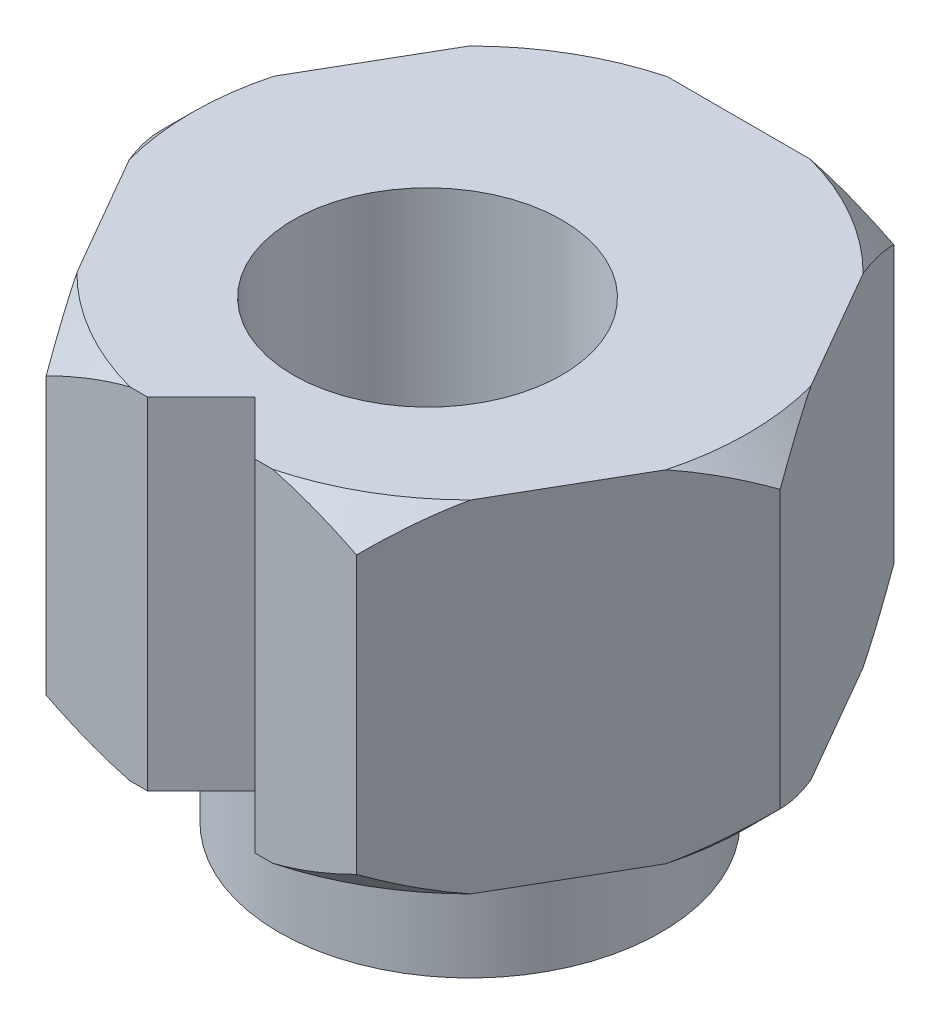
SolidWorks part; units mm, degrees
material "AISI 304"
ref_plane "Front Plane" through (0, 0, 0) normal (0, 0, 1) x (1, 0, 0)
ref_plane "Top Plane" through (0, 0, 0) normal (0, 1, 0) x (1, 0, 0)
ref_plane "Right Plane" through (0, 0, 0) normal (1, 0, 0) x (0, 0, -1)
sketch "Sketch1" plane through (0, 0, 0) normal (0, 1, 0) x (1, 0, 0)
  line L1 (5.7735, 0) -> (2.8868, 5)
  line L2 (2.8868, 5) -> (-2.8868, 5)
  line L3 (-2.8868, 5) -> (-5.7735, 0)
  line L4 (-5.7735, 0) -> (-2.8868, -5)
  line L5 (-2.8868, -5) -> (2.8868, -5)
  line L6 (2.8868, -5) -> (5.7735, 0)
  circle A0 centre (0, 0) radius 5 construction
  dimension "D1" = 10
extrude "Boss-Extrude1" add sketch "Sketch1" along normal blind 6.35
sketch "Sketch3" plane through (0, 0, 0) normal (0, -1, 0) x (1, 0, 0)
  circle A0 centre (0, 0) radius 3.555
  dimension "D1" = 7.11
extrude "Boss-Extrude3" add sketch "Sketch3" along normal blind 2.5
sketch "Sketch4" plane through (0, 6.35, 0) normal (0, 1, 0) x (1, 0, 0)
  line L0 (0, 0) -> (0, -0.79) construction
  circle A0 centre (0, -0.79) radius 2.5
  dimension "D1" = 5
  dimension "D2" = 0.79
extrude "Cut-Extrude1" cut sketch "Sketch4" against normal through all
sketch "Sketch5" plane through (0, 0, 0) normal (0, -1, 0) x (-1, 0, 0)
  line L0 (2.8868, -5) -> (-2.8868, -5) construction
  line L1 (-1, -5) -> (1, -5)
  line L2 (-1, -5) -> (0, -4)
  line L4 (1, -5) -> (0, -4)
  line L5 (0, -5) -> (0, 0) construction
  dimension "D1" = 2
extrude "Cut-Extrude2" cut sketch "Sketch5" against normal through all
sketch "Sketch6" plane through (0, 0, 0) normal (0, 0, 1) x (1, 0, 0)
  line L0 (0, 0) -> (0, 6.4706) construction
  line L1 (5.1735, 6.35) -> (5.7735, 6.35)
  line L2 (2.8868, 6.35) -> (5.7735, 6.35) construction
  line L3 (5.7735, 6.35) -> (5.7735, 5.75)
  line L4 (5.7735, 6.35) -> (5.7735, 0) construction
  line L5 (5.7735, 5.75) -> (5.1735, 6.35)
  line L6 (5.7735, 3.175) -> (6.8775, 3.175) construction
  line L7 (5.7735, 6.35) -> (5.7735, 0) construction
  line L8 (5.7735, 0.6) -> (5.1735, 0)
  line L9 (5.7735, 0) -> (5.7735, 0.6)
  line L10 (5.1735, 0) -> (5.7735, 0)
  dimension "D1" = 0.6
revolve "Cut-Revolve1" cut sketch "Sketch6" angle 360 about L0
